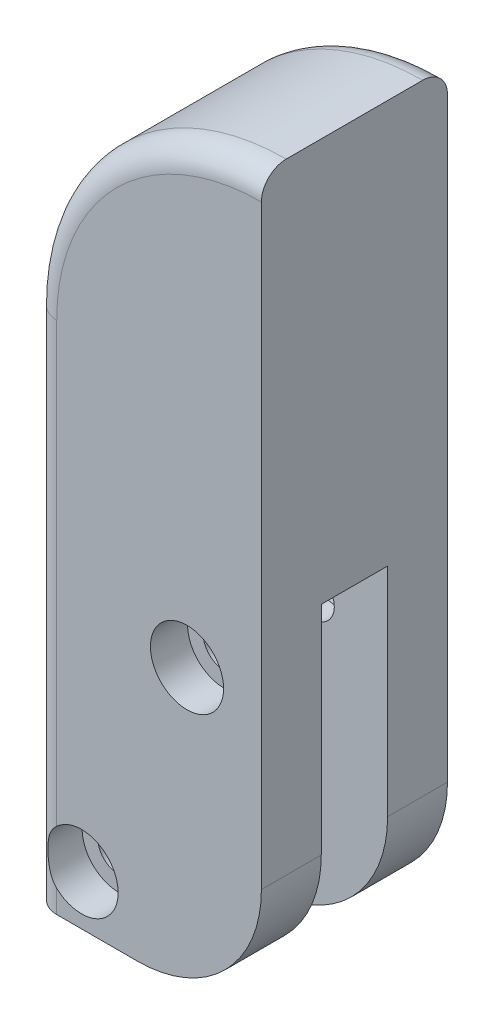
SolidWorks part; units mm, degrees
ref_plane "Alzado" through (0, 0, 0) normal (0, 0, 1) x (1, 0, 0)
ref_plane "Planta" through (0, 0, 0) normal (0, 1, 0) x (1, 0, 0)
ref_plane "Vista lateral" through (0, 0, 0) normal (1, 0, 0) x (0, 0, -1)
sketch "Croquis1" plane through (0, 0, 0) normal (0, 0, 1) x (1, 0, 0)
  line L1 (9.25, -20.75) -> (-9.25, -20.75)
  line L2 (9.25, -20.75) -> (9.25, 20.75)
  line L4 (-9.25, -20.75) -> (-9.25, 20.75)
  line L5 (9.25, -20.75) -> (-9.25, 20.75) construction
  line L6 (9.25, 20.75) -> (9.25, 39.25)
  arc A0 (9.25, 39.25) -> (-9.25, 20.75) centre (9.25, 20.75) ccw
  point P0 (0, 0)
  dimension "D1" = 60
  dimension "D2" = 18.5
extrude "Saliente-Extruir1" add sketch "Croquis1" along normal blind 15
sketch "Croquis2" plane through (9.25, 0, 0) normal (1, 0, 0) x (0, 0, -1)
  line L0 (-15, -20.75) -> (0, -20.75) construction
  line L1 (-10.175, 6.75) -> (-4.825, 6.75)
  line L2 (-10.175, 6.75) -> (-10.175, -20.75)
  line L3 (-10.175, -20.75) -> (-4.825, -20.75)
  line L4 (-4.825, 6.75) -> (-4.825, -20.75)
  line L5 (-10.175, 6.75) -> (-4.825, -20.75) construction
  line L6 (-10.175, -20.75) -> (-4.825, 6.75) construction
  point P0 (-7.5, -7)
  point P7 (-7.5, -20.75)
  dimension "D1" = 5.35
  dimension "D2" = 27.5
extrude "Cortar-Extruir1" cut sketch "Croquis2" against normal blind 30
sketch "Croquis3" plane through (0, 0, 15) normal (0, 0, 1) x (1, 0, 0)
  line L0 (-9.25, 20.75) -> (-9.25, -20.75) construction
  line L1 (-9.25, -20.75) -> (9.25, -20.75) construction
  circle A0 centre (3.25, 1.75) radius 1.7
  circle A1 centre (-5.25, -16.75) radius 1.7
  point P8 (-8.755, -14.6272)
  dimension "D5" = 3.4
  dimension "D1" = 4
  dimension "D2" = 4
  dimension "D3" = 22.5
  dimension "D4" = 12.5
extrude "Cortar-Extruir2" cut sketch "Croquis3" against normal blind 30
fillet "Redondeo1" radius 10 2 edges at (9.25, -20.75, 2.4125) (9.25, -20.75, 12.5875)
fillet "Redondeo2" radius 2 4 edges at (-9.25, 0, 0) (-3.8315, 33.8315, 0) (-9.25, 0, 15) (-3.8315, 33.8315, 15)
sketch "Croquis4" plane through (0, 0, 15) normal (0, 0, 1) x (1, 0, 0)
  circle A0 centre (3.25, 1.75) radius 2.95
  circle A1 centre (-5.25, -16.75) radius 2.95
  dimension "D1" = 5.9
extrude "Cortar-Extruir3" cut sketch "Croquis4" against normal blind 3
sketch "Croquis5" plane through (0, 0, 0) normal (0, 0, -1) x (-1, 0, 0)
  line L0 (-9.25, -10.75) -> (-9.25, 37.25) construction
  line L1 (-0.3488, 3.425) -> (-3.25, 5.1)
  line L2 (-3.25, 5.1) -> (-6.1512, 3.425)
  line L3 (-6.1512, 3.425) -> (-6.1512, 0.075)
  line L4 (-6.1512, 0.075) -> (-3.25, -1.6)
  line L5 (-3.25, -1.6) -> (-0.3488, 0.075)
  line L6 (-0.3488, 0.075) -> (-0.3488, 3.425)
  line L7 (5.25, -13.4) -> (2.3488, -15.075)
  line L8 (2.3488, -15.075) -> (2.3488, -18.425)
  line L9 (2.3488, -18.425) -> (5.25, -20.1)
  line L10 (5.25, -20.1) -> (8.1512, -18.425)
  line L11 (8.1512, -18.425) -> (8.1512, -15.075)
  line L12 (8.1512, -15.075) -> (5.25, -13.4)
  circle A0 centre (-3.25, 1.75) radius 3.35 construction
  circle A1 centre (5.25, -16.75) radius 3.35 construction
  dimension "D1" = 6.7
extrude "Cortar-Extruir4" cut sketch "Croquis5" against normal blind 3
